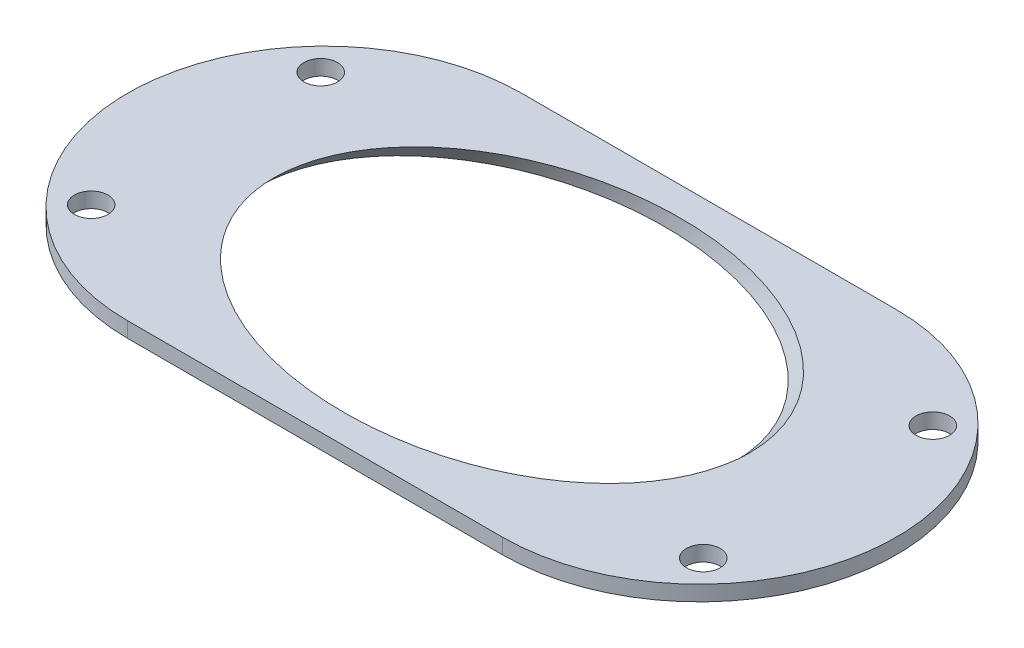
SolidWorks part; units mm, degrees
material "7075-T6 (SN)"
ref_plane "Front Plane" through (0, 0, 0) normal (0, 0, 1) x (1, 0, 0)
ref_plane "Top Plane" through (0, 0, 0) normal (0, 1, 0) x (1, 0, 0)
ref_plane "Right Plane" through (0, 0, 0) normal (1, 0, 0) x (0, 0, -1)
sketch "Sketch1" plane through (0, 0, 0) normal (0, 1, 0) x (1, 0, 0)
  line L0 (-12.25, 0) -> (12.25, 0) construction
  line L1 (-12.25, 12.875) -> (12.25, 12.875)
  line L2 (-12.25, -12.875) -> (12.25, -12.875)
  line L3 (12.25, 12.875) -> (12.25, -12.875) construction
  arc A0 (-12.25, 12.875) -> (-12.25, -12.875) centre (-12.25, 0) ccw
  arc A1 (12.25, -12.875) -> (12.25, 12.875) centre (12.25, 0) ccw
  point P2 (0, 0)
  dimension "D1" = 24.5
  dimension "D2" = 25.75
extrude "Boss-Extrude1" add sketch "Sketch1" along normal blind 1
ref_plane "Plane1" through (6.125, 6.125, 0) normal (0.7071, 0.7071, 0) x (0, 0, 1)
sketch "Sketch2" plane through (6.125, 6.125, 0) normal (0.7071, 0.7071, 0) x (0, 0, 1)
  line L0 (-12.875, 7.955) -> (-12.875, -9.3692) construction
  circle A0 centre (0, -0.7071) radius 11
  point P6 (-12.875, -0.7071)
  dimension "D1" = 22
extrude "Cut-Extrude1" cut sketch "Sketch2" against normal through all both and the other way through all
hole_wizard "M2 Clearance Hole1" positions "Sketch3" profile "Sketch4" hole size "M2" standard "DIN" end condition up to next
sketch "Sketch3" plane through (0, 1, 0) normal (0, 1, 0) x (1, 0, 0)
  line L8 (-20, 7.5) -> (20, 7.5) construction
  line L9 (-20, 7.5) -> (-20, -7.5) construction
  line L10 (-20, -7.5) -> (20, -7.5) construction
  line L11 (20, 7.5) -> (20, -7.5) construction
  line L12 (-20, 7.5) -> (20, -7.5) construction
  line L13 (-20, -7.5) -> (20, 7.5) construction
  point P0 (-20, 7.5)
  point P2 (-20, -7.5)
  point P4 (20, -7.5)
  point P6 (20, 7.5)
  dimension "D1" = 15
  dimension "D2" = 40
sketch "Sketch4" plane through (-20, 1, -7.5) normal (1, 0, 0) x (0, 0, 1)
  line L0 (0, 0) -> (0, 1)
  line L1 (0, 1) -> (1.1, 1)
  line L2 (1.1, 1) -> (1.1, 0)
  line L5 (1.1, 0) -> (0, 0)
  line L11 (0, -6.35) -> (0, 107.95) construction
  dimension "Thru Hole Dia." = 2.2
  dimension "Thru Hole Depth" = 1
